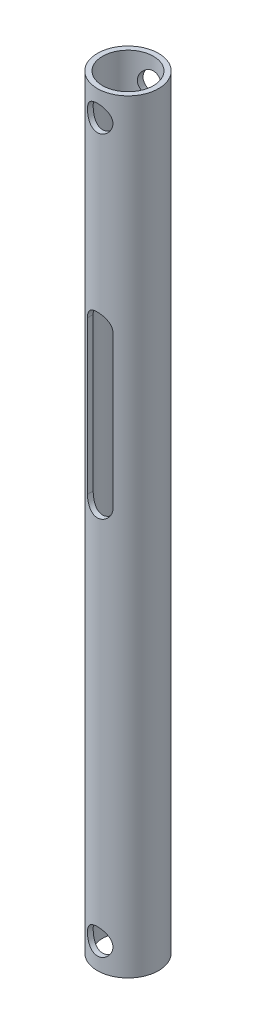
SolidWorks part; units mm, degrees
material "7075-T6 (SN)"
ref_plane "Płaszczyzna przednia" through (0, 0, 0) normal (0, 0, 1) x (1, 0, 0)
ref_plane "Płaszczyzna górna" through (0, 0, 0) normal (0, 1, 0) x (1, 0, 0)
ref_plane "Płaszczyzna prawa" through (0, 0, 0) normal (1, 0, 0) x (0, 0, -1)
sketch "Szkic1" plane through (0, 0, 0) normal (0, 1, 0) x (1, 0, 0)
  circle A0 centre (0, 0) radius 5
  circle A1 centre (0, 0) radius 6
  dimension "D1" = 10
  dimension "D2" = 1
extrude "Dodanie-wyciągnięcie1" add sketch "Szkic1" along normal blind 150
sketch "Szkic3" plane through (0, 0, 0) normal (0, 0, 1) x (1, 0, 0)
  line L0 (0, 79.5) -> (0, 109.5) construction
  line L1 (-2.5, 79.5) -> (-2.5, 109.5)
  line L2 (2.5, 79.5) -> (2.5, 109.5)
  line L3 (6, 150) -> (-6, 150) construction
  line L4 (-6, 0) -> (6, 0) construction
  line L5 (6, 0) -> (6, 150) construction
  line L6 (-6, 150) -> (-6, 0) construction
  arc A0 (-2.5, 79.5) -> (2.5, 79.5) centre (0, 79.5) ccw
  arc A1 (2.5, 109.5) -> (-2.5, 109.5) centre (0, 109.5) ccw
  circle A2 centre (0, 145) radius 2.5
  circle A3 centre (0, 5) radius 2.5
  point P3 (0, 94.5)
  dimension "D1" = 5
  dimension "D2" = 5
  dimension "D8" = 3.5
  dimension "D3" = 5
  dimension "D4" = 5
  dimension "D5" = 30
  dimension "D6" = 74.5
  dimension "D7" = 5
  dimension "D9" = 6
extrude "Wytnij-wyciągnięcie2" cut sketch "Szkic3" against normal through all and the other way through all
